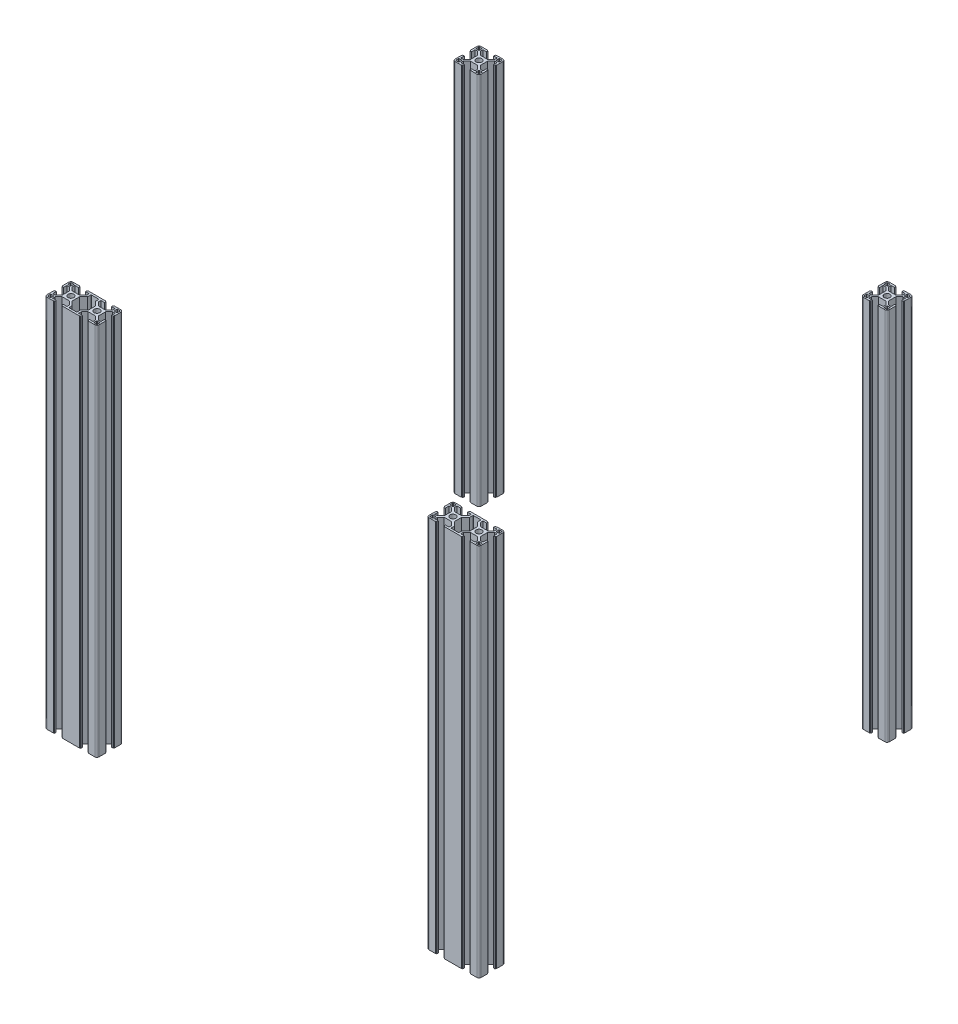
SolidWorks part; units mm, degrees
ref_plane "Front" through (0, 0, 0) normal (0, 0, 1) x (1, 0, 0)
ref_plane "Top" through (0, 0, 0) normal (0, 1, 0) x (1, 0, 0)
ref_plane "Right" through (0, 0, 0) normal (1, 0, 0) x (0, 0, -1)
sketch3d "3D草图1"
  line L1 (-11877.4357, 11295.5774, 7.2664) -> (-11407.4357, 11295.5774, 7.2664)
  line L2 (-11877.4357, 11295.5774, 7.2664) -> (-11877.4357, 10864.5774, 7.2664)
  line L3 (-11877.4357, 10864.5774, 7.2664) -> (-11407.4357, 10864.5774, 7.2664)
  line L4 (-11407.4357, 11295.5774, 7.2664) -> (-11407.4357, 10864.5774, 7.2664)
  line L5 (-11407.4357, 11295.5774, 7.2664) -> (-11407.4357, 11295.5774, -462.7336)
  line L7 (-11407.4357, 11295.5774, -462.7336) -> (-11407.4357, 10864.5774, -462.7336)
  line L8 (-11877.4357, 11295.5774, -462.7336) -> (-11877.4357, 10864.5774, -462.7336)
  line L9 (-11877.4357, 10864.5774, -462.7336) -> (-11407.4357, 10864.5774, -462.7336)
  line L10 (-11877.4357, 11295.5774, -462.7336) -> (-11407.4357, 11295.5774, -462.7336)
  line L12 (-11877.4357, 11295.5774, 7.2664) -> (-11877.4357, 11295.5774, -462.7336)
  line L13 (-11877.4357, 10864.5774, 7.2664) -> (-11877.4357, 10864.5774, -462.7336)
  line L14 (-11407.4357, 10864.5774, 7.2664) -> (-11407.4357, 10864.5774, -462.7336)
  dimension "D1" = 470
  dimension "D2" = 431
  dimension "D3" = 470
other "Qy铝型材 QY-8-3060(1)"
ref_plane "基准面1"
sketch "Sketch1" plane through (-11877.4357, 11295.5774, 7.2664) normal (0, -1, 0) x (1, 0, 0)
  line L0 (-5.2, 15) -> (-5.2, 14.5)
  line L1 (-5.2, 14.5) -> (-4.1, 14.5)
  line L2 (-4.1, 14.5) -> (-4.1, 12.8)
  line L3 (-4.1, 12.8) -> (-8.25, 12.8)
  line L4 (-12.5, -15) -> (-5.2, -15)
  line L5 (-15, -12.5) -> (-15, -5.325)
  line L6 (24.8, 15) -> (5.2, 15)
  line L7 (15, 12.625) -> (15, 5.325) construction
  line L8 (0, 14.8756) -> (0, 0) construction
  line L9 (0, 0) -> (14.1675, 0) construction
  line L10 (-8.25, 12.8) -> (-8.25, 9.8056)
  line L11 (-8.25, 9.8056) -> (-4.2444, 5.8)
  line L12 (-4.2444, 5.8) -> (4.2444, 5.8)
  line L13 (8.25, 9.8056) -> (4.2444, 5.8)
  line L14 (8.25, 12.8) -> (8.25, 9.8056)
  line L15 (4.1, 12.8) -> (8.25, 12.8)
  line L16 (4.1, 14.5) -> (4.1, 12.8)
  line L17 (5.2, 14.5) -> (4.1, 14.5)
  line L18 (5.2, 15) -> (5.2, 14.5)
  line L19 (-5.2, 15) -> (-12.5, 15)
  line L20 (15.25, 5.325) -> (14.75, 5.325) construction
  line L21 (14.75, 5.325) -> (14.75, 4.225) construction
  line L22 (14.75, 4.225) -> (13.05, 4.225) construction
  line L23 (13.05, 4.225) -> (13.05, 8.375) construction
  line L24 (13.05, 8.375) -> (10.0556, 8.375) construction
  line L25 (10.45, 8.8944) -> (5.8, 4.2444)
  line L26 (5.8, 4.2444) -> (5.8, -4.2444)
  line L27 (10.45, -12.3) -> (10.45, -8.8944)
  line L28 (19.55, -12.3) -> (19.55, -8.8944)
  line L29 (10.45, 12.3) -> (10.45, 8.8944)
  line L30 (0, 0) -> (-4.1823, 4.1823) construction
  line L31 (19.55, 12.3) -> (19.55, 8.8944)
  line L32 (10.45, -8.8944) -> (5.8, -4.2444)
  line L33 (5.2, -15) -> (5.2, -14.5)
  line L34 (5.2, -14.5) -> (4.1, -14.5)
  line L35 (4.1, -14.5) -> (4.1, -12.8)
  line L36 (4.1, -12.8) -> (8.25, -12.8)
  line L37 (8.25, -12.8) -> (8.25, -9.8056)
  line L38 (8.25, -9.8056) -> (4.2444, -5.8)
  line L39 (4.2444, -5.8) -> (-4.2444, -5.8)
  line L40 (-8.25, -9.8056) -> (-4.2444, -5.8)
  line L41 (-8.25, -12.8) -> (-8.25, -9.8056)
  line L42 (-4.1, -12.8) -> (-8.25, -12.8)
  line L43 (-4.1, -14.5) -> (-4.1, -12.8)
  line L44 (-5.2, -14.5) -> (-4.1, -14.5)
  line L45 (-5.2, -15) -> (-5.2, -14.5)
  line L46 (-15, -5.325) -> (-14.5, -5.325)
  line L47 (-14.5, -5.325) -> (-14.5, -4.225)
  line L48 (-14.5, -4.225) -> (-12.8, -4.225)
  line L49 (-12.8, -4.225) -> (-12.8, -8.25)
  line L50 (-12.8, -8.25) -> (-9.8056, -8.25)
  line L51 (-9.8056, -8.25) -> (-5.8, -4.2444)
  line L52 (-5.8, -4.2444) -> (-5.8, 4.2444)
  line L53 (-9.8056, 8.25) -> (-5.8, 4.2444)
  line L54 (-12.8, 8.25) -> (-9.8056, 8.25)
  line L55 (-12.8, 3.975) -> (-12.8, 8.25)
  line L56 (-14.5, 3.975) -> (-12.8, 3.975)
  line L57 (-14.5, 5.075) -> (-14.5, 3.975)
  line L58 (-15, 5.075) -> (-14.5, 5.075)
  line L59 (5.2, -15) -> (24.8, -15)
  line L60 (-15, 5.075) -> (-15, 12.5)
  line L61 (19.55, -8.8944) -> (24.2, -4.2444)
  line L62 (10.95, -12.8) -> (19.05, -12.8)
  line L63 (-13, 13.5) -> (-10.25, 13.5)
  line L64 (-13.5, 13) -> (-13.5, 10.25)
  line L65 (-13, 9.75) -> (-10.25, 9.75)
  line L66 (-9.75, 13) -> (-9.75, 10.25)
  line L67 (-13.5, 13.5) -> (-9.75, 9.75) construction
  line L68 (-13.5, 9.75) -> (-9.75, 13.5) construction
  line L69 (21.75, -12.8) -> (25.9, -12.8)
  line L70 (21.75, 12.8) -> (25.9, 12.8)
  line L71 (10.95, 12.8) -> (19.05, 12.8)
  line L74 (-13.5, -9.75) -> (-9.75, -13.5) construction
  line L75 (-13.5, -13.5) -> (-9.75, -9.75) construction
  line L76 (-9.75, -13) -> (-9.75, -10.25)
  line L77 (-13, -9.75) -> (-10.25, -9.75)
  line L78 (-13.5, -13) -> (-13.5, -10.25)
  line L79 (-13, -13.5) -> (-10.25, -13.5)
  line L88 (43.5, -13.5) -> (39.75, -9.75) construction
  line L89 (43.5, -9.75) -> (39.75, -13.5) construction
  line L91 (43.5, 9.75) -> (39.75, 13.5) construction
  line L92 (43.5, 13.5) -> (39.75, 9.75) construction
  line L94 (30, 0) -> (15.8325, 0) construction
  line L95 (30, 14.8756) -> (30, 0) construction
  line L100 (43, -13.5) -> (40.25, -13.5)
  line L101 (43.5, -13) -> (43.5, -10.25)
  line L102 (43, -9.75) -> (40.25, -9.75)
  line L103 (39.75, -13) -> (39.75, -10.25)
  line L108 (39.75, 13) -> (39.75, 10.25)
  line L109 (43, 9.75) -> (40.25, 9.75)
  line L110 (43.5, 13) -> (43.5, 10.25)
  line L111 (43, 13.5) -> (40.25, 13.5)
  line L112 (45, 5.075) -> (45, 12.5)
  line L114 (45, 5.075) -> (44.5, 5.075)
  line L115 (44.5, 5.075) -> (44.5, 3.975)
  line L116 (44.5, 3.975) -> (42.8, 3.975)
  line L117 (42.8, 3.975) -> (42.8, 8.25)
  line L118 (42.8, 8.25) -> (39.8056, 8.25)
  line L119 (39.8056, 8.25) -> (35.8, 4.2444)
  line L120 (35.8, -4.2444) -> (35.8, 4.2444)
  line L121 (39.8056, -8.25) -> (35.8, -4.2444)
  line L122 (42.8, -8.25) -> (39.8056, -8.25)
  line L123 (42.8, -4.225) -> (42.8, -8.25)
  line L124 (44.5, -4.225) -> (42.8, -4.225)
  line L125 (44.5, -5.325) -> (44.5, -4.225)
  line L126 (45, -5.325) -> (44.5, -5.325)
  line L127 (35.2, -15) -> (35.2, -14.5)
  line L128 (35.2, -14.5) -> (34.1, -14.5)
  line L129 (34.1, -14.5) -> (34.1, -12.8)
  line L130 (34.1, -12.8) -> (38.25, -12.8)
  line L131 (38.25, -12.8) -> (38.25, -9.8056)
  line L132 (38.25, -9.8056) -> (34.2444, -5.8)
  line L133 (25.7556, -5.8) -> (34.2444, -5.8)
  line L134 (21.75, -9.8056) -> (25.7556, -5.8)
  line L135 (21.75, -12.8) -> (21.75, -9.8056)
  line L137 (25.9, -14.5) -> (25.9, -12.8)
  line L138 (24.8, -14.5) -> (25.9, -14.5)
  line L139 (24.8, -15) -> (24.8, -14.5)
  line L145 (24.2, 4.2444) -> (24.2, -4.2444)
  line L146 (19.55, 8.8944) -> (24.2, 4.2444)
  line L148 (16.95, 4.225) -> (16.95, 8.375) construction
  line L149 (15.25, 4.225) -> (16.95, 4.225) construction
  line L150 (15.25, 5.325) -> (15.25, 4.225) construction
  line L151 (35.2, 15) -> (42.5, 15)
  line L152 (24.8, 15) -> (24.8, 14.5)
  line L153 (24.8, 14.5) -> (25.9, 14.5)
  line L154 (25.9, 14.5) -> (25.9, 12.8)
  line L156 (21.75, 12.8) -> (21.75, 9.8056)
  line L157 (21.75, 9.8056) -> (25.7556, 5.8)
  line L158 (34.2444, 5.8) -> (25.7556, 5.8)
  line L159 (38.25, 9.8056) -> (34.2444, 5.8)
  line L160 (38.25, 12.8) -> (38.25, 9.8056)
  line L162 (45, -12.5) -> (45, -5.325)
  line L163 (42.5, -15) -> (35.2, -15)
  line L164 (34.1, 12.8) -> (38.25, 12.8)
  line L165 (34.1, 14.5) -> (34.1, 12.8)
  line L166 (35.2, 14.5) -> (34.1, 14.5)
  line L167 (35.2, 15) -> (35.2, 14.5)
  circle A0 centre (0, 0) radius 3.35
  arc A1 (-15, 12.5) -> (-12.5, 15) centre (-12.5, 12.5) cw
  arc A2 (10.45, 12.3) -> (10.95, 12.8) centre (10.95, 12.3) cw
  arc A3 (-12.5, -15) -> (-15, -12.5) centre (-12.5, -12.5) cw
  arc A4 (19.55, 12.3) -> (19.05, 12.8) centre (19.05, 12.3) ccw
  arc A5 (-13.5, 10.25) -> (-13, 9.75) centre (-13, 10.25) ccw
  arc A6 (-9.75, 10.25) -> (-10.25, 9.75) centre (-10.25, 10.25) cw
  arc A7 (-9.75, 13) -> (-10.25, 13.5) centre (-10.25, 13) ccw
  arc A8 (-13.5, 13) -> (-13, 13.5) centre (-13, 13) cw
  arc A9 (19.55, -12.3) -> (19.05, -12.8) centre (19.05, -12.3) cw
  arc A10 (10.45, -12.3) -> (10.95, -12.8) centre (10.95, -12.3) ccw
  arc A13 (-13.5, -13) -> (-13, -13.5) centre (-13, -13) ccw
  arc A14 (-9.75, -13) -> (-10.25, -13.5) centre (-10.25, -13) cw
  arc A15 (-9.75, -10.25) -> (-10.25, -9.75) centre (-10.25, -10.25) ccw
  arc A16 (-13.5, -10.25) -> (-13, -9.75) centre (-13, -10.25) cw
  arc A25 (43.5, -10.25) -> (43, -9.75) centre (43, -10.25) ccw
  arc A26 (39.75, -10.25) -> (40.25, -9.75) centre (40.25, -10.25) cw
  arc A27 (39.75, -13) -> (40.25, -13.5) centre (40.25, -13) ccw
  arc A28 (43.5, -13) -> (43, -13.5) centre (43, -13) cw
  arc A33 (43.5, 13) -> (43, 13.5) centre (43, 13) ccw
  arc A34 (39.75, 13) -> (40.25, 13.5) centre (40.25, 13) cw
  arc A35 (39.75, 10.25) -> (40.25, 9.75) centre (40.25, 10.25) ccw
  arc A36 (43.5, 10.25) -> (43, 9.75) centre (43, 10.25) cw
  arc A38 (42.5, -15) -> (45, -12.5) centre (42.5, -12.5) ccw
  arc A40 (45, 12.5) -> (42.5, 15) centre (42.5, 12.5) ccw
  circle A41 centre (30, 0) radius 3.35
  point P0 (0, 0)
  point P4 (0, 0)
  point P5 (-15, -15)
  point P6 (15, -15)
  point P7 (15, 15)
  point P8 (-15, 15)
  point P13 (-11.625, 11.625)
  point P36 (-15, 15)
  point P39 (15, 15)
  point P102 (10.45, 12.8)
  point P105 (19.55, 12.8)
  point P108 (19.55, -12.8)
  point P111 (10.45, -12.8)
  point P134 (-11.625, -11.625)
  point P285 (41.625, -11.625)
  point P287 (45, 15)
  point P288 (41.625, 11.625)
  point P289 (45, -15)
  dimension "D1" = 9.2
  dimension "D2" = 15
  dimension "D3" = 8.2
  dimension "D4" = 8.2
  dimension "D5" = 15
  dimension "D6" = 6.7
  dimension "D7" = 2.5
  dimension "D8" = 2.2
  dimension "D12" = 1.5
  dimension "D13" = 1.5
  dimension "D14" = 16.5
  dimension "D9" = 2.2
  dimension "D17" = 0.5
  dimension "D18" = 2.2
  dimension "D19" = 0.5
  dimension "D10" = 1.5
  dimension "D11" = 1.5
  dimension "D15" = 0.5
  dimension "D16" = 45
  dimension "D20" = 10.4
  dimension "D21" = 0.5
  dimension "D22" = 3.975
  dimension "D23" = 5.075
  dimension "D24" = 2.2
  dimension "D25" = 9.2
  dimension "D26" = 9.2
  dimension "D27" = 16.5
  dimension "D28" = 0.5
  dimension "D29" = 10.4
other "Qy铝型材 QY-8-3030(1)"
ref_plane "基准面2" through (-11407.4357, 11295.5774, -462.7336) normal (0, -1, 0) x (1, 0, 0)
sketch "Sketch11" plane through (-11407.4357, 11295.5774, -462.7336) normal (0, -1, 0) x (1, 0, 0)
  line L0 (-5.2, 15) -> (-5.2, 14.5)
  line L1 (-5.2, 14.5) -> (-4.1, 14.5)
  line L2 (-4.1, 14.5) -> (-4.1, 12.8)
  line L3 (-4.1, 12.8) -> (-8.25, 12.8)
  line L4 (-12.5, -15) -> (-5.2, -15)
  line L5 (-15, -12.5) -> (-15, -5.2)
  line L6 (12.5, 15) -> (5.2, 15)
  line L7 (15, 12.5) -> (15, 5.2)
  line L8 (0, 14.8756) -> (0, 0) construction
  line L9 (0, 0) -> (14.1675, 0) construction
  line L10 (-8.25, 12.8) -> (-8.25, 9.8)
  line L11 (-8.25, 9.8) -> (-4.25, 5.8)
  line L12 (-4.25, 5.8) -> (4.25, 5.8)
  line L13 (8.25, 9.8) -> (4.25, 5.8)
  line L14 (8.25, 12.8) -> (8.25, 9.8)
  line L15 (4.1, 12.8) -> (8.25, 12.8)
  line L16 (4.1, 14.5) -> (4.1, 12.8)
  line L17 (5.2, 14.5) -> (4.1, 14.5)
  line L18 (5.2, 15) -> (5.2, 14.5)
  line L19 (-5.2, 15) -> (-12.5, 15)
  line L20 (15, 5.2) -> (14.5, 5.2)
  line L21 (14.5, 5.2) -> (14.5, 4.1)
  line L22 (14.5, 4.1) -> (12.8, 4.1)
  line L23 (12.8, 4.1) -> (12.8, 8.25)
  line L24 (12.8, 8.25) -> (9.8, 8.25)
  line L25 (9.8, 8.25) -> (5.8, 4.25)
  line L26 (5.8, 4.25) -> (5.8, -4.25)
  line L27 (9.8, -8.25) -> (5.8, -4.25)
  line L28 (12.8, -8.25) -> (9.8, -8.25)
  line L29 (12.8, -4.1) -> (12.8, -8.25)
  line L30 (14.5, -4.1) -> (12.8, -4.1)
  line L31 (14.5, -5.2) -> (14.5, -4.1)
  line L32 (15, -5.2) -> (14.5, -5.2)
  line L33 (5.2, -15) -> (5.2, -14.5)
  line L34 (5.2, -14.5) -> (4.1, -14.5)
  line L35 (4.1, -14.5) -> (4.1, -12.8)
  line L36 (4.1, -12.8) -> (8.25, -12.8)
  line L37 (8.25, -12.8) -> (8.25, -9.8)
  line L38 (8.25, -9.8) -> (4.25, -5.8)
  line L39 (4.25, -5.8) -> (-4.25, -5.8)
  line L40 (-8.25, -9.8) -> (-4.25, -5.8)
  line L41 (-8.25, -12.8) -> (-8.25, -9.8)
  line L42 (-4.1, -12.8) -> (-8.25, -12.8)
  line L43 (-4.1, -14.5) -> (-4.1, -12.8)
  line L44 (-5.2, -14.5) -> (-4.1, -14.5)
  line L45 (-5.2, -15) -> (-5.2, -14.5)
  line L46 (-15, -5.2) -> (-14.5, -5.2)
  line L47 (-14.5, -5.2) -> (-14.5, -4.1)
  line L48 (-14.5, -4.1) -> (-12.8, -4.1)
  line L49 (-12.8, -4.1) -> (-12.8, -8.25)
  line L50 (-12.8, -8.25) -> (-9.8, -8.25)
  line L51 (-9.8, -8.25) -> (-5.8, -4.25)
  line L52 (-5.8, -4.25) -> (-5.8, 4.25)
  line L53 (-9.8, 8.25) -> (-5.8, 4.25)
  line L54 (-12.8, 8.25) -> (-9.8, 8.25)
  line L55 (-12.8, 4.1) -> (-12.8, 8.25)
  line L56 (-14.5, 4.1) -> (-12.8, 4.1)
  line L57 (-14.5, 5.2) -> (-14.5, 4.1)
  line L58 (-15, 5.2) -> (-14.5, 5.2)
  line L59 (5.2, -15) -> (12.5, -15)
  line L60 (-15, 5.2) -> (-15, 12.5)
  line L61 (15, -5.2) -> (15, -12.5)
  line L62 (13.5, 9.75) -> (9.75, 13.5) construction
  line L63 (-13, 13.5) -> (-10.25, 13.5)
  line L64 (-13.5, 13) -> (-13.5, 10.25)
  line L65 (-13, 9.75) -> (-10.25, 9.75)
  line L66 (-9.75, 13) -> (-9.75, 10.25)
  line L67 (-13.5, 13.5) -> (-9.75, 9.75) construction
  line L68 (-13.5, 9.75) -> (-9.75, 13.5) construction
  line L69 (13.5, 13.5) -> (9.75, 9.75) construction
  line L70 (9.75, 13) -> (9.75, 10.25)
  line L71 (13, 9.75) -> (10.25, 9.75)
  line L72 (13.5, 13) -> (13.5, 10.25)
  line L73 (13, 13.5) -> (10.25, 13.5)
  line L74 (-13.5, -9.75) -> (-9.75, -13.5) construction
  line L75 (-13.5, -13.5) -> (-9.75, -9.75) construction
  line L76 (-9.75, -13) -> (-9.75, -10.25)
  line L77 (-13, -9.75) -> (-10.25, -9.75)
  line L78 (-13.5, -13) -> (-13.5, -10.25)
  line L79 (-13, -13.5) -> (-10.25, -13.5)
  line L80 (13.5, -13.5) -> (9.75, -9.75) construction
  line L81 (13.5, -9.75) -> (9.75, -13.5) construction
  line L82 (13, -13.5) -> (10.25, -13.5)
  line L83 (13.5, -13) -> (13.5, -10.25)
  line L84 (13, -9.75) -> (10.25, -9.75)
  line L85 (9.75, -13) -> (9.75, -10.25)
  circle A0 centre (0, 0) radius 3.35
  arc A1 (-15, 12.5) -> (-12.5, 15) centre (-12.5, 12.5) cw
  arc A2 (15, 12.5) -> (12.5, 15) centre (12.5, 12.5) ccw
  arc A3 (-12.5, -15) -> (-15, -12.5) centre (-12.5, -12.5) cw
  arc A4 (12.5, -15) -> (15, -12.5) centre (12.5, -12.5) ccw
  arc A5 (-13.5, 10.25) -> (-13, 9.75) centre (-13, 10.25) ccw
  arc A6 (-9.75, 10.25) -> (-10.25, 9.75) centre (-10.25, 10.25) cw
  arc A7 (-9.75, 13) -> (-10.25, 13.5) centre (-10.25, 13) ccw
  arc A8 (-13.5, 13) -> (-13, 13.5) centre (-13, 13) cw
  arc A9 (13.5, 13) -> (13, 13.5) centre (13, 13) ccw
  arc A10 (9.75, 13) -> (10.25, 13.5) centre (10.25, 13) cw
  arc A11 (9.75, 10.25) -> (10.25, 9.75) centre (10.25, 10.25) ccw
  arc A12 (13.5, 10.25) -> (13, 9.75) centre (13, 10.25) cw
  arc A13 (-13.5, -13) -> (-13, -13.5) centre (-13, -13) ccw
  arc A14 (-9.75, -13) -> (-10.25, -13.5) centre (-10.25, -13) cw
  arc A15 (-9.75, -10.25) -> (-10.25, -9.75) centre (-10.25, -10.25) ccw
  arc A16 (-13.5, -10.25) -> (-13, -9.75) centre (-13, -10.25) cw
  arc A17 (13.5, -10.25) -> (13, -9.75) centre (13, -10.25) ccw
  arc A18 (9.75, -10.25) -> (10.25, -9.75) centre (10.25, -10.25) cw
  arc A19 (9.75, -13) -> (10.25, -13.5) centre (10.25, -13) ccw
  arc A20 (13.5, -13) -> (13, -13.5) centre (13, -13) cw
  point P0 (-10, 0)
  point P1 (10, 0)
  point P2 (0, 10)
  point P3 (0, -10)
  point P4 (0, 0)
  point P5 (-15, -15)
  point P6 (15, -15)
  point P7 (15, 15)
  point P8 (-15, 15)
  point P13 (-11.625, 11.625)
  point P36 (-15, 15)
  point P39 (15, 15)
  point P117 (11.625, 11.625)
  point P134 (-11.625, -11.625)
  point P151 (11.625, -11.625)
  point P152 (0, 0)
  dimension "D1" = 9.2
  dimension "D2" = 4
  dimension "D3" = 10.4
  dimension "D4" = 8.2
  dimension "D5" = 30
  dimension "D6" = 6.7
  dimension "D7" = 2.5
  dimension "D8" = 8.5
  dimension "D12" = 1.5
  dimension "D13" = 1.5
  dimension "D14" = 16.5
  dimension "D9" = 2.2
  dimension "D17" = 0.5
  dimension "D10" = 1.5
  dimension "D11" = 1.5
  dimension "D15" = 0.5
  dimension "D16" = 135
